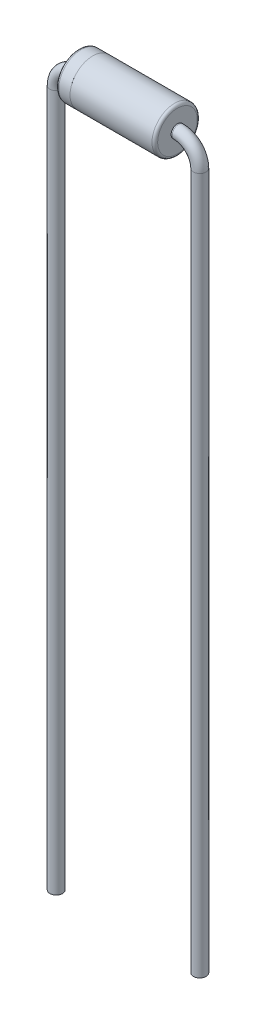
SolidWorks part; units mm, degrees
material "Plain Carbon Steel"
ref_plane "Front Plane" through (0, 0, 0) normal (0, 0, 1) x (1, 0, 0)
ref_plane "Top Plane" through (0, 0, 0) normal (0, 1, 0) x (1, 0, 0)
ref_plane "Right Plane" through (0, 0, 0) normal (1, 0, 0) x (0, 0, -1)
sketch "Sketch1" plane through (0, 0, 0) normal (0, 0, 1) x (1, 0, 0)
  line L0 (-1.79, 0) -> (1.79, 0)
  line L1 (-2.54, -0.75) -> (-2.54, -25.4)
  line L2 (2.54, -0.75) -> (2.54, -25.4)
  line L3 (-2.54, -25.4) -> (2.54, -25.4) construction
  line L4 (0, 0) -> (0, -25.4) construction
  arc A0 (-1.79, 0) -> (-2.54, -0.75) centre (-1.79, -0.75) ccw
  arc A1 (1.79, 0) -> (2.54, -0.75) centre (1.79, -0.75) cw
  dimension "D2" = 0.75
  dimension "D1" = 5.08
  dimension "D3" = 25.4
ref_plane "Plane1" through (-2.54, -25.4, 0) normal (0, -1, 0) x (-1, 0, 0)
sketch "Sketch2" plane through (-2.54, -25.4, 0) normal (0, -1, 0) x (-1, 0, 0)
  circle A0 centre (0, 0) radius 0.225
  dimension "D1" = 0.45
sweep "Sweep1" add profiles "Sketch2" path "Sketch1"
sketch "Sketch3" plane through (0, 0, 0) normal (0, 0, 1) x (1, 0, 0)
  line L0 (0, 0) -> (0, 0.3) construction
  line L1 (-1.4, 0.5) -> (-0.1, 0.5)
  line L2 (-1.5, 0.4) -> (-1.5, 0)
  line L3 (-1.5, 0) -> (1.5, 0)
  line L4 (1.5, 0.4) -> (1.5, 0)
  line L5 (0.1, 0.5) -> (1.4, 0.5)
  line L7 (-0.05, 0.45) -> (-0.05, 0.3)
  line L8 (-0.05, 0.3) -> (0.05, 0.3)
  line L9 (0.05, 0.45) -> (0.05, 0.3)
  line L10 (-0.05, 0.5) -> (0.05, 0.5) construction
  line L11 (-0.1, 0.5) -> (-0.05, 0.5) construction
  line L12 (0.05, 0.5) -> (0.1, 0.5) construction
  arc A0 (-1.4, 0.5) -> (-1.5, 0.4) centre (-1.4, 0.4) ccw
  arc A1 (1.4, 0.5) -> (1.5, 0.4) centre (1.4, 0.4) cw
  arc A2 (-0.1, 0.5) -> (-0.05, 0.45) centre (-0.1, 0.45) cw
  arc A3 (0.1, 0.5) -> (0.05, 0.45) centre (0.1, 0.45) ccw
  dimension "D3" = 0.1
  dimension "D6" = 0.05
  dimension "D1" = 3
  dimension "D2" = 0.5
  dimension "D4" = 0.1
  dimension "D5" = 0.2
revolve "Revolve1" add sketch "Sketch3" angle 360 about L3
sketch "Sketch4" plane through (0, 0, 0) normal (0, 0, 1) x (1, 0, 0)
  line L0 (-1.25, 0) -> (-1.25, 0.8)
  line L1 (-1.25, 0.8) -> (1.65, 0.8)
  line L3 (-1.25, 0) -> (1.75, 0)
  line L4 (1.75, 0.7) -> (1.75, 0)
  line L5 (-1.17, 0.08) -> (1.67, 0.08) construction
  line L6 (1.67, 0.7) -> (1.67, 0.08) construction
  line L7 (-1.17, 0.72) -> (1.65, 0.72) construction
  line L8 (-1.17, 0.08) -> (-1.17, 0.72) construction
  arc A1 (1.65, 0.8) -> (1.75, 0.7) centre (1.65, 0.7) cw
  arc A2 (1.65, 0.72) -> (1.67, 0.7) centre (1.65, 0.7) cw construction
  dimension "D3" = 1.25
  dimension "D4" = 0.1
  dimension "D1" = 1.75
  dimension "D2" = 0.8
  dimension "D5" = 0.08
revolve "Revolve3" add sketch "Sketch4" angle 360 about L3
sketch "Sketch5" plane through (0, 0, 0) normal (0, 0, 1) x (1, 0, 0)
  line L0 (-1.33, 0.72) -> (-1.65, 0.72)
  line L1 (-1.25, 0) -> (-1.75, 0)
  line L2 (-1.25, 0) -> (-1.25, 0.8)
  line L3 (-1.25, 0.8) -> (-1.65, 0.8)
  line L4 (-1.75, 0) -> (-1.75, 0.7)
  line L5 (-1.67, 0.08) -> (-1.67, 0.7)
  line L6 (-1.33, 0.08) -> (-1.67, 0.08)
  line L7 (-1.33, 0.08) -> (-1.33, 0.72)
  arc A0 (-1.65, 0.8) -> (-1.75, 0.7) centre (-1.65, 0.7) ccw
  arc A1 (-1.65, 0.72) -> (-1.67, 0.7) centre (-1.65, 0.7) ccw
  point P4 (-1.25, 0.8)
  dimension "D2" = 0.1
  dimension "D1" = 1.75
  dimension "D3" = 0.08
revolve "Revolve4" add sketch "Sketch5" angle 360 about L1
